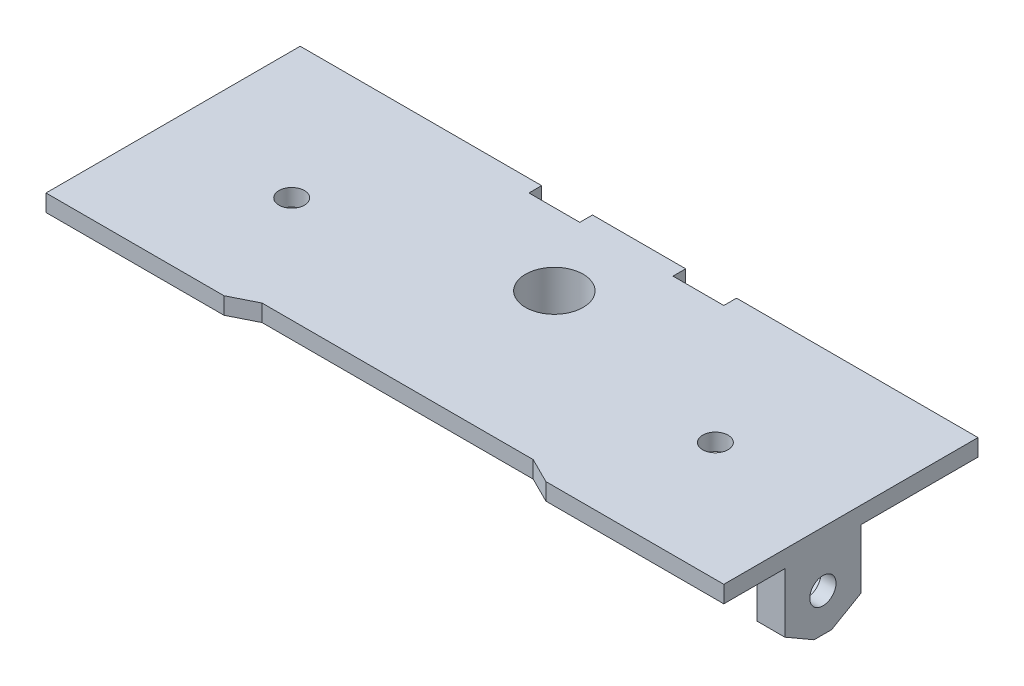
SolidWorks part; units mm, degrees
ref_plane "Front Plane" through (0, 0, 0) normal (0, 0, 1) x (1, 0, 0)
ref_plane "Top Plane" through (0, 0, 0) normal (0, 1, 0) x (1, 0, 0)
ref_plane "Right Plane" through (0, 0, 0) normal (1, 0, 0) x (0, 0, -1)
sketch "Sketch1" plane through (0, 0, 0) normal (0, 1, 0) x (1, 0, 0)
  line L0 (0, 0) -> (50, 0) construction
  line L1 (0, 14) -> (50, 14) construction
  line L2 (0, -14) -> (50, -14) construction
  line L3 (0, 14) -> (25, 6) construction
  line L4 (25, 6) -> (50, 14) construction
  line L5 (25, 6) -> (25, 14) construction
  line L6 (28.6587, 1.2446) -> (41.463, 11.096)
  line L7 (21.3413, 1.2446) -> (8.537, 11.096)
  circle A0 centre (0, 0) radius 14 construction
  circle A1 centre (50, 0) radius 14 construction
  circle A2 centre (25, 6) radius 6 construction
  arc A3 (8.537, 11.096) -> (0, -14) centre (0, 0) ccw
  arc A4 (41.463, 11.096) -> (50, -14) centre (50, 0) cw
  arc A5 (21.3413, 1.2446) -> (28.6587, 1.2446) centre (25, 6) ccw
  dimension "D1" = 28
  dimension "D2" = 12
  dimension "D3" = 50
  dimension "D4" = 8
sketch "Sketch2" plane through (0, 0, 0) normal (0, 1, 0) x (1, 0, 0)
  line L1 (-15, 16) -> (65, 16)
  line L2 (25, -11) -> (25, -14) construction
  line L3 (-15, -14) -> (65, -14)
  line L5 (0, -14) -> (50, -14) construction
  line L9 (65, -14) -> (65, 16)
  line L10 (-15, -14) -> (-15, 16)
  line L11 (25, -14) -> (25, 0) construction
  line L12 (0, 0) -> (50, 0) construction
  circle A4 centre (0, 0) radius 1.5
  circle A5 centre (50, 0) radius 1.5
  circle A6 centre (25, 6) radius 3.4
extrude "Boss-Extrude1" add sketch "Sketch2" along normal blind 2
sketch "Sketch3" plane through (0, 2, 0) normal (0, 1, 0) x (1, 0, 0)
  line L0 (0, -14) -> (50, -14) construction
  line L1 (6, -14) -> (44, -14)
  line L2 (6, -14) -> (9, -12.5)
  line L3 (9, -12.5) -> (41, -12.5)
  line L4 (44, -14) -> (41, -12.5)
  line L6 (13.5, 16) -> (19.5, 16)
  line L7 (13.5, 16) -> (13.5, 14.5)
  line L8 (13.5, 14.5) -> (19.5, 14.5)
  line L9 (19.5, 16) -> (19.5, 14.5)
  line L10 (16.5, 16) -> (25, 16) construction
  line L11 (30.5, 16) -> (36.5, 16)
  line L12 (30.5, 16) -> (30.5, 14.5)
  line L13 (30.5, 14.5) -> (36.5, 14.5)
  line L14 (36.5, 16) -> (36.5, 14.5)
  line L15 (25, 16) -> (33.5, 16) construction
  line L16 (25, -12.5) -> (25, -14) construction
  line L17 (65, 16) -> (-15, 16) construction
extrude "Boss-Extrude2" add sketch "Sketch3" along normal blind 9
sketch "Sketch9" plane through (0, 2, 0) normal (0, 1, 0) x (1, 0, 0)
  circle A2 centre (50, 0) radius 1.5
  circle A3 centre (50, 0) radius 1.5
  circle A4 centre (50, 0) radius 4
  circle A5 centre (0, 0) radius 1.5
  circle A6 centre (0, 0) radius 1.5
  circle A7 centre (0, 0) radius 4
extrude "Boss-Extrude4" add sketch "Sketch9" along normal blind 7
sketch "Sketch4" plane through (0, 0, 0) normal (0, -1, 0) x (1, 0, 0)
  circle A2 centre (25, -6) radius 6
  circle A3 centre (25, -6) radius 6
  circle A5 centre (25, -6) radius 3.4
  circle A6 centre (25, -6) radius 3.4
  dimension "D1" = 0
  dimension "D2" = 0
extrude "Boss-Extrude3" add sketch "Sketch4" along normal blind 4
sketch "Sketch10" plane through (0, 9, 0) normal (0, 1, 0) x (1, 0, 0)
  circle A2 centre (50, 0) radius 1.5
  circle A3 centre (50, 0) radius 1.5
  circle A5 centre (50, 0) radius 4
  circle A6 centre (50, 0) radius 4
  circle A8 centre (0, 0) radius 1.5
  circle A9 centre (0, 0) radius 1.5
  circle A11 centre (0, 0) radius 4
  circle A12 centre (0, 0) radius 4
  dimension "D1" = 0
  dimension "D2" = 0
  dimension "D3" = 0
  dimension "D4" = 0
extrude "Cut-Extrude7" cut sketch "Sketch10" against normal up to surface (7 mm away) up to face at (50, 2, -4)
sketch "Sketch11" plane through (0, 11, 0) normal (0, 1, 0) x (1, 0, 0)
  line L4 (36.5, 16) -> (30.5, 16)
  line L5 (36.5, 16) -> (30.5, 16)
  line L8 (9, -12.5) -> (6, -14)
  line L9 (6, -14) -> (44, -14)
  line L10 (44, -14) -> (41, -12.5)
  line L11 (41, -12.5) -> (9, -12.5)
  line L12 (9, -12.5) -> (6, -14)
  line L13 (6, -14) -> (44, -14)
  line L14 (44, -14) -> (41, -12.5)
  line L15 (41, -12.5) -> (9, -12.5)
  line L20 (30.5, 16) -> (30.5, 14.5)
  line L21 (30.5, 14.5) -> (36.5, 14.5)
  line L22 (36.5, 14.5) -> (36.5, 16)
  line L24 (30.5, 16) -> (30.5, 14.5)
  line L25 (30.5, 14.5) -> (36.5, 14.5)
  line L26 (36.5, 14.5) -> (36.5, 16)
  line L32 (13.5, 16) -> (13.5, 14.5)
  line L33 (13.5, 14.5) -> (19.5, 14.5)
  line L34 (19.5, 14.5) -> (19.5, 16)
  line L35 (19.5, 16) -> (13.5, 16)
  line L36 (13.5, 16) -> (13.5, 14.5)
  line L37 (13.5, 14.5) -> (19.5, 14.5)
  line L38 (19.5, 14.5) -> (19.5, 16)
  line L39 (19.5, 16) -> (13.5, 16)
  dimension "D1" = 0
  dimension "D2" = 0
  dimension "D3" = 0
extrude "Cut-Extrude8" cut sketch "Sketch11" against normal up to surface (11 mm away) up to face at (0, 0, 1.5)
sketch "Sketch12" plane through (0, 0, 0) normal (0, -1, 0) x (1, 0, 0)
  line L6 (-15, -16) -> (-15, 14) construction
  line L7 (-15, 6.8071) -> (-11.7, 6.8071)
  line L8 (-15, 6.8071) -> (-15, -2.1929)
  line L9 (-15, -2.1929) -> (-11.7, -2.1929)
  line L10 (-11.7, 6.8071) -> (-11.7, -2.1929)
  line L11 (65, 14) -> (65, -16) construction
  line L12 (65, 6.8071) -> (61.7, 6.8071)
  line L13 (65, 6.8071) -> (65, -2.1929)
  line L14 (65, -2.1929) -> (61.7, -2.1929)
  line L15 (61.7, 6.8071) -> (61.7, -2.1929)
  line L16 (-11.7, 2.3071) -> (61.7, 2.3071) construction
  dimension "D3" = 9
  dimension "D4" = 9
  dimension "D5" = 3.3
  dimension "D6" = 3.3
extrude "Boss-Extrude5" add sketch "Sketch12" along normal blind 9
sketch "Sketch15" plane through (-11.7, 0, 0) normal (1, 0, 0) x (0, 0, -1)
  line L0 (-6.8071, -9) -> (2.1929, 0) construction
  line L2 (-2.3071, -1.2668) -> (-5.1071, -2.8834)
  line L3 (-5.1071, -2.8834) -> (-5.1071, -6.1166)
  line L4 (-5.1071, -6.1166) -> (-2.3071, -7.7332)
  line L5 (-2.3071, -7.7332) -> (0.4929, -6.1166)
  line L6 (0.4929, -6.1166) -> (0.4929, -2.8834)
  line L7 (0.4929, -2.8834) -> (-2.3071, -1.2668)
  circle A0 centre (-2.3071, -4.5) radius 2.8 construction
  dimension "D1" = 5.6
extrude "Cut-Extrude11" cut sketch "Sketch15" against normal blind 1.5
sketch "Sketch16" plane through (61.7, 0, 0) normal (-1, 0, 0) x (0, 0, 1)
  line L12 (2.3071, -1.2668) -> (-0.4929, -2.8834)
  line L13 (5.1071, -2.8834) -> (2.3071, -1.2668)
  line L14 (5.1071, -6.1166) -> (5.1071, -2.8834)
  line L15 (2.3071, -7.7332) -> (5.1071, -6.1166)
  line L16 (-0.4929, -6.1166) -> (2.3071, -7.7332)
  line L17 (-0.4929, -2.8834) -> (-0.4929, -6.1166)
  line L18 (2.3071, -1.2668) -> (-0.4929, -2.8834)
  line L19 (5.1071, -2.8834) -> (2.3071, -1.2668)
  line L20 (5.1071, -6.1166) -> (5.1071, -2.8834)
  line L21 (2.3071, -7.7332) -> (5.1071, -6.1166)
  line L22 (-0.4929, -6.1166) -> (2.3071, -7.7332)
  line L23 (-0.4929, -2.8834) -> (-0.4929, -6.1166)
  dimension "D1" = 0
extrude "Cut-Extrude12" cut sketch "Sketch16" against normal blind 1.5
sketch "Sketch18" plane through (-15, 0, 0) normal (-1, 0, 0) x (0, 0, 1)
  line L0 (-2.1929, 0) -> (6.8071, -9) construction
  circle A0 centre (2.3071, -4.5) radius 1.55
  dimension "D1" = 3.1
extrude "Cut-Extrude13" cut sketch "Sketch18" against normal through all
chamfer "Chamfer1" distance 2 angle 60 4 edges at (63.35, -9, 6.8071) (63.35, -9, -2.1929) (-13.35, -9, -2.1929) (-13.35, -9, 6.8071)
equation "\"D4@Sketch2\"=\"D3@Sketch2\""
equation "\"D8@Sketch3\"=\"D5@Sketch3\""
equation "\"D4@Sketch9\"=\"D3@Sketch9\""
